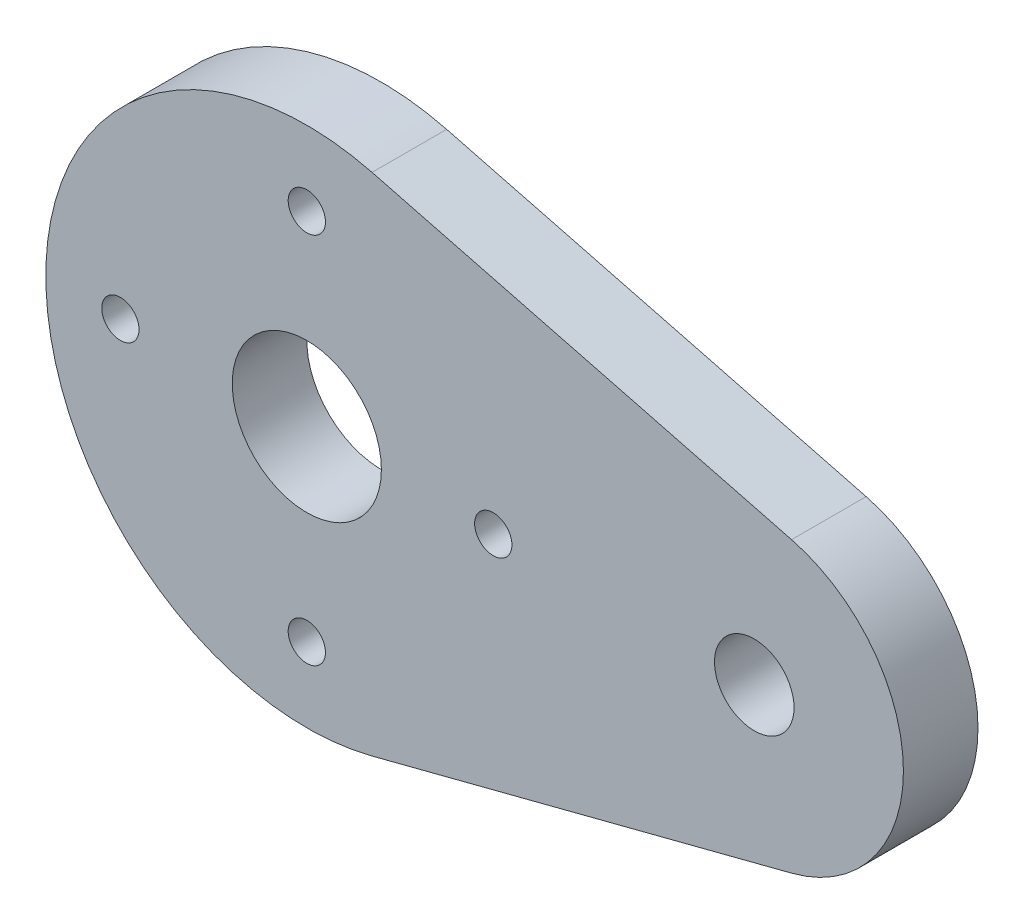
SolidWorks part; units mm, degrees
ref_plane "前视基准面" through (0, 0, 0) normal (0, 0, 1) x (1, 0, 0)
ref_plane "上视基准面" through (0, 0, 0) normal (0, 1, 0) x (1, 0, 0)
ref_plane "右视基准面" through (0, 0, 0) normal (1, 0, 0) x (0, 0, -1)
sketch "草图1" plane through (0, 0, 0) normal (0, 0, 1) x (1, 0, 0)
  line L0 (0, 0) -> (18, 0) construction
  line L1 (2.625, 10.1666) -> (19.5, 5.8095)
  line L2 (2.625, -10.1666) -> (19.5, -5.8095)
  arc A0 (2.625, 10.1666) -> (2.625, -10.1666) centre (0, 0) ccw
  circle A1 centre (18, 0) radius 1.6
  arc A2 (19.5, -5.8095) -> (19.5, 5.8095) centre (18, 0) ccw
  circle A3 centre (0, 0) radius 3
  dimension "D1" = 21
  dimension "D3" = 3.2
  dimension "D4" = 12
  dimension "D5" = 6
  dimension "D2" = 18
extrude "凸台-拉伸1" add sketch "草图1" along normal blind 3
sketch "草图2" plane through (0, 0, 3) normal (0, 0, 1) x (1, 0, 0)
  line L0 (0, 0) -> (0, 7.5) construction
  line L1 (0, 0) -> (-10.5, 0) construction
  circle A0 centre (0, 7.5) radius 0.75
  arc A1 (2.625, 10.1666) -> (2.625, -10.1666) centre (0, 0) ccw construction
  circle A2 centre (7.5, 0) radius 0.75
  circle A3 centre (0, -7.5) radius 0.75
  circle A4 centre (-7.5, 0) radius 0.75
  point P17 (0, 0)
  dimension "D2" = 1.5
  dimension "D1" = 15
  dimension "D3" = 4
extrude "切除-拉伸1" cut sketch "草图2" against normal up to next
